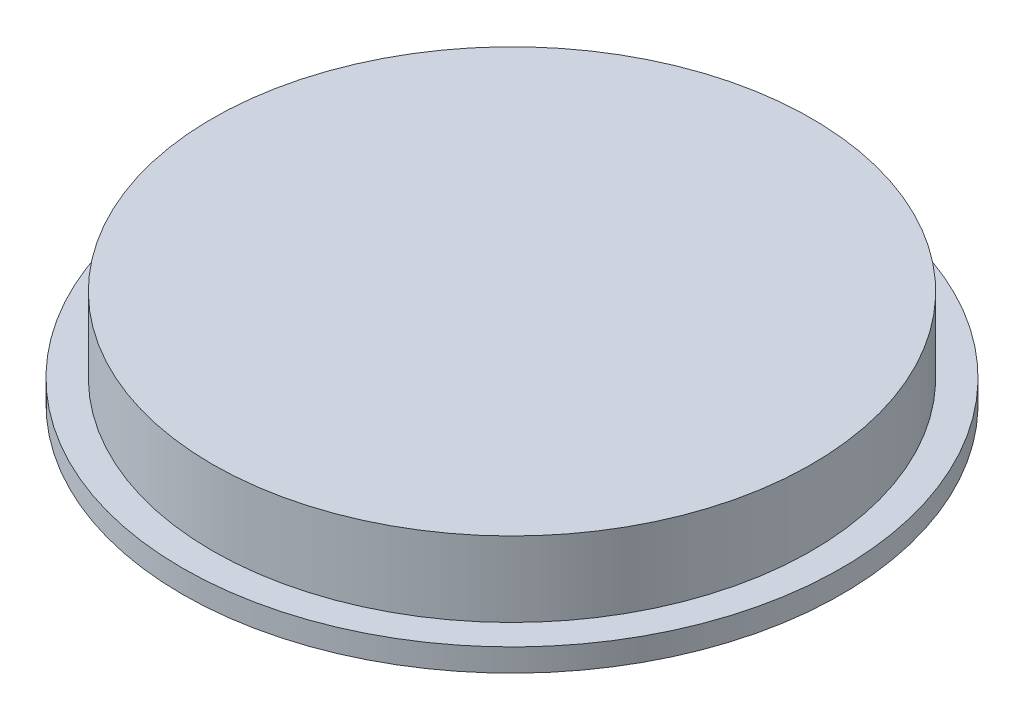
SolidWorks part; units mm, degrees
other "Camera1"
ref_plane "Front Plane" through (0, 0, 0) normal (0, 0, 1) x (1, 0, 0)
ref_plane "Top Plane" through (0, 0, 0) normal (0, 1, 0) x (1, 0, 0)
ref_plane "Right Plane" through (0, 0, 0) normal (1, 0, 0) x (0, 0, -1)
sketch "Sketch1" plane through (0, 0, 0) normal (0, 0, 1) x (1, 0, 0)
  line L0 (0, 45.2932) -> (0, -50.5102) construction
  line L1 (0, 13.5169) -> (50.8, 13.5169)
  line L4 (55.88, -3.0367) -> (55.88, 0.8169)
  line L5 (55.88, 0.8169) -> (50.8, 0.8169)
  line L6 (50.8, 0.8169) -> (50.8, 13.5169)
  line L7 (55.88, -3.0367) -> (47.1598, -3.0367)
  line L8 (47.1598, -3.0367) -> (38.1, 1.6707)
  line L9 (38.1, 1.6707) -> (0, 1.6707)
  line L10 (0, 13.5169) -> (0, 1.6707)
  dimension "D1" = 38.1
  dimension "D2" = 12.7
  dimension "D3" = 50.8
  dimension "D4" = 5.08
revolve "Revolve1" add sketch "Sketch1" angle 360 about L0
ref_plane "mate to root" through (0, 0.8169, 0) normal (0, 1, 0) x (1, 0, 0)
ref_plane "inside of roof " through (0, 13.5169, 0) normal (0, 1, 0) x (1, 0, 0)
